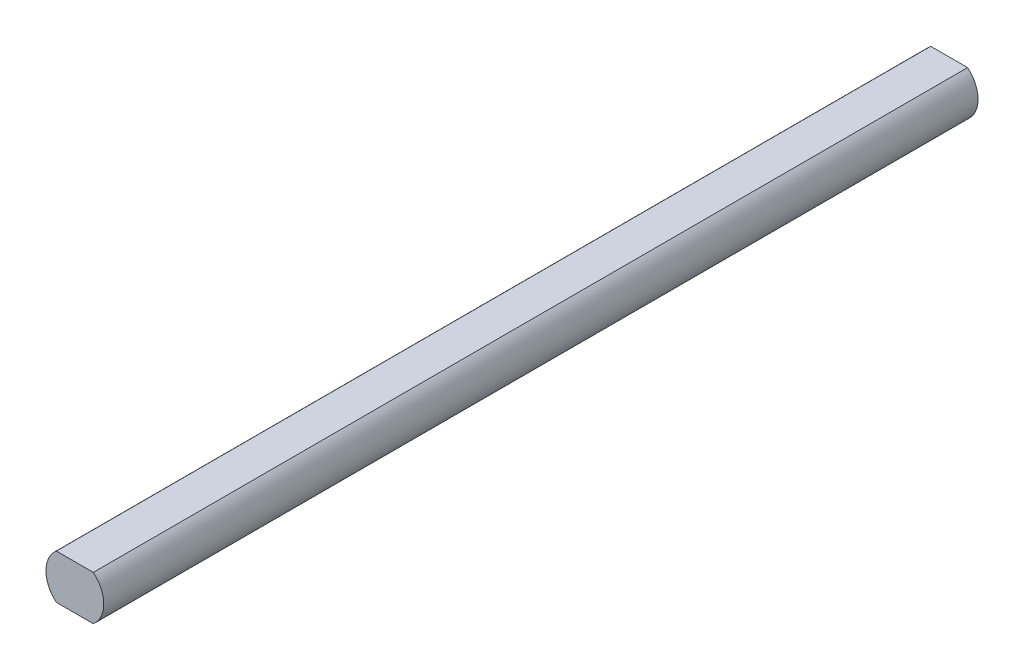
SolidWorks part; units mm, degrees
ref_plane "Plano frontal" through (0, 0, 0) normal (0, 0, 1) x (1, 0, 0)
ref_plane "Plano superior" through (0, 0, 0) normal (0, 1, 0) x (1, 0, 0)
ref_plane "Plano direito" through (0, 0, 0) normal (1, 0, 0) x (0, 0, -1)
sketch "Esboço1" plane through (0, 0, 0) normal (0, 0, 1) x (1, 0, 0)
  line L0 (-2.492, 3) -> (2.492, 3)
  line L1 (-3.9, 0) -> (3.9, 0) construction
  line L2 (2.492, -3) -> (-2.492, -3)
  arc A0 (-2.492, 3) -> (-2.492, -3) centre (0, 0) ccw
  arc A1 (2.492, -3) -> (2.492, 3) centre (0, 0) ccw
  dimension "D1" = 3.9
  dimension "D2" = 6
extrude "Ressalto-extrusão1" add sketch "Esboço1" along normal blind 118
